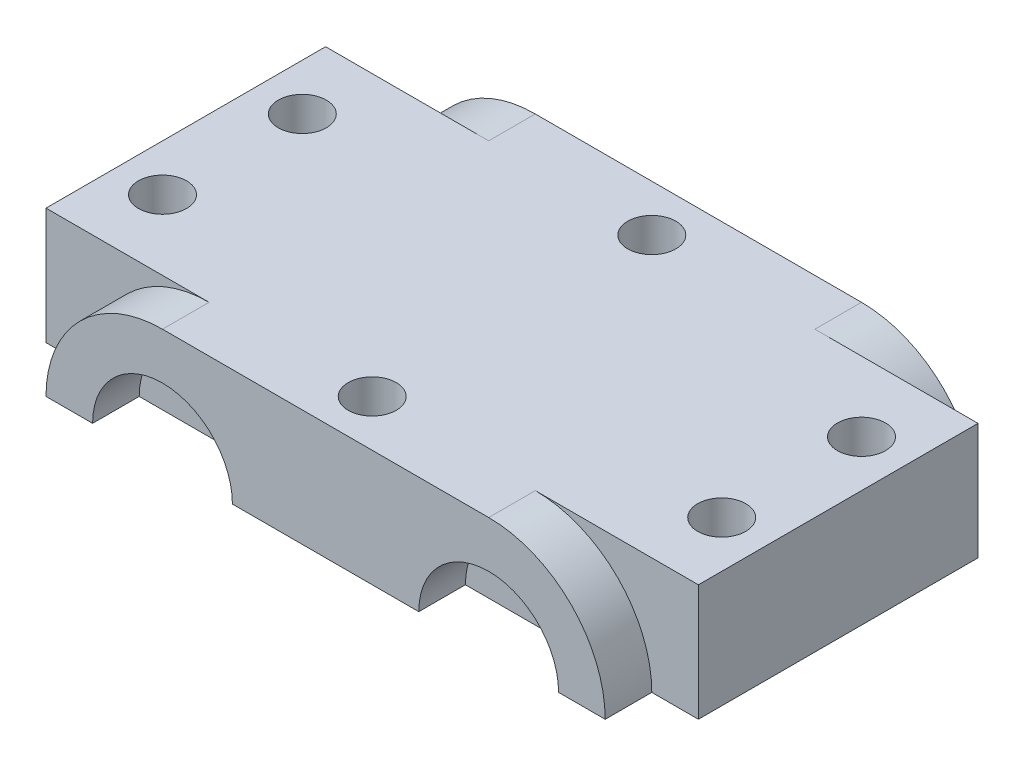
SolidWorks part; units mm, degrees
ref_plane "Front Plane" through (0, 0, 0) normal (0, 0, 1) x (1, 0, 0)
ref_plane "Top Plane" through (0, 0, 0) normal (0, 1, 0) x (1, 0, 0)
ref_plane "Right Plane" through (0, 0, 0) normal (1, 0, 0) x (0, 0, -1)
sketch "Sketch2" plane through (0, 0, 0) normal (0, 0, 1) x (1, 0, 0)
  line L0 (0, 26.7229) -> (0, -26.2693) construction
  line L1 (-140.3723, 0) -> (134.412, 0) construction
  line L3 (-88.9, -15.875) -> (88.9, -15.875)
  line L4 (-88.9, -15.875) -> (-88.9, 15.875)
  line L5 (-88.9, 15.875) -> (88.9, 15.875)
  line L6 (88.9, -15.875) -> (88.9, 15.875)
  dimension "high blue base" = 31.75
  dimension "length blue base" = 177.8
extrude "base-blue" add sketch "Sketch2" against normal blind 76.2
sketch "Sketch3" plane through (0, 15.875, 0) normal (0, 1, 0) x (1, 0, 0)
  line L0 (-76.2, 100.8581) -> (-76.2, -13.1656) construction
  line L1 (0, 91.8903) -> (0, -23.6954) construction
  line L2 (76.2, 91.8903) -> (76.2, -23.6954) construction
  line L3 (-121.6384, 57.15) -> (113.8285, 57.15) construction
  line L4 (88.9, 76.2) -> (-88.9, 76.2) construction
  line L5 (-121.6384, 19.05) -> (119.8811, 19.05) construction
  line L6 (88.9, 0) -> (-88.9, 0) construction
  line L7 (-88.9, 76.2) -> (-88.9, 0) construction
  circle A0 centre (-76.2, 19.05) radius 6.5532
  circle A2 centre (-76.2, 57.15) radius 6.5532
  circle A4 centre (76.2, 57.15) radius 6.5532
  circle A5 centre (76.2, 19.05) radius 6.5532
  circle A6 centre (0, 0) radius 6.5532
  circle A7 centre (0, 76.2) radius 6.5532
  dimension "red cyl6" = 13.1064
  dimension "D2" = 152.4
  dimension "red cyl5" = 13.1064
  dimension "D3" = 19.05
  dimension "red cyl" = 13.1064
  dimension "red cyl2" = 13.1064
  dimension "red cyl4" = 13.1064
  dimension "red cyl3" = 13.1064
  dimension "cyl dist" = 38.1
  dimension "dist cyl and blue base" = 12.7
sketch "Sketch4" plane through (0, 0, 0) normal (0, 0, 1) x (1, 0, 0)
  line L0 (-116.6906, -15.875) -> (130.4482, -15.875) construction
  line L1 (0, 23.7778) -> (0, -29.6898) construction
  line L2 (-88.9, -15.875) -> (88.9, -15.875) construction
  line L3 (-121.6384, 15.875) -> (113.8285, 15.875) construction
  line L4 (44.45, 15.875) -> (-44.45, 15.875)
  line L5 (-76.2, -15.875) -> (-63.5, -15.875)
  line L6 (-25.4, -15.875) -> (25.4, -15.875)
  line L7 (63.5, -15.875) -> (76.2, -15.875)
  line L8 (-88.9, 15.875) -> (-88.9, -15.875) construction
  line L9 (88.9, -15.875) -> (88.9, 15.875) construction
  arc A0 (76.2, -15.875) -> (44.45, 15.875) centre (44.45, -15.875) ccw
  arc A1 (-44.45, 15.875) -> (-76.2, -15.875) centre (-44.45, -15.875) ccw
  arc A2 (-63.5, -15.875) -> (-25.4, -15.875) centre (-44.45, -15.875) cw
  arc A3 (25.4, -15.875) -> (63.5, -15.875) centre (44.45, -15.875) cw
  dimension "D1" = 31.75
  dimension "D2" = 25.4
  dimension "D4" = 19.05
  dimension "D5" = 88.9
  dimension "D7" = 12.7
extrude "base-yellow-R" add sketch "Sketch4" along normal blind 12.7
sketch "Sketch5" plane through (0, 0, -76.2) normal (0, 0, -1) x (-1, 0, 0)
  line L3 (76.2, -15.875) -> (63.5, -15.875) construction
  line L4 (25.4, -15.875) -> (-25.4, -15.875) construction
  line L5 (-63.5, -15.875) -> (-76.2, -15.875) construction
  line L6 (-44.45, 15.875) -> (44.45, 15.875) construction
  line L7 (76.2, -15.875) -> (63.5, -15.875)
  line L12 (25.4, -15.875) -> (-25.4, -15.875)
  line L13 (-63.5, -15.875) -> (-76.2, -15.875)
  line L19 (-44.45, 15.875) -> (44.45, 15.875)
  arc A5 (76.2, -15.875) -> (44.45, 15.875) centre (44.45, -15.875) ccw construction
  arc A6 (63.5, -15.875) -> (25.4, -15.875) centre (44.45, -15.875) ccw construction
  arc A7 (-25.4, -15.875) -> (-63.5, -15.875) centre (-44.45, -15.875) ccw construction
  arc A8 (-44.45, 15.875) -> (-76.2, -15.875) centre (-44.45, -15.875) ccw construction
  arc A9 (76.2, -15.875) -> (44.45, 15.875) centre (44.45, -15.875) ccw
  arc A11 (63.5, -15.875) -> (25.4, -15.875) centre (44.45, -15.875) ccw
  arc A12 (-25.4, -15.875) -> (-63.5, -15.875) centre (-44.45, -15.875) ccw
  arc A13 (-44.45, 15.875) -> (-76.2, -15.875) centre (-44.45, -15.875) ccw
extrude "base-yellow-L" add sketch "Sketch5" along normal blind 12.7
extrude "cyl-red" cut sketch "Sketch3" against normal through all
equation "\"high blue base@Sketch2\"=\"length blue base@Sketch2\"/5.6"
